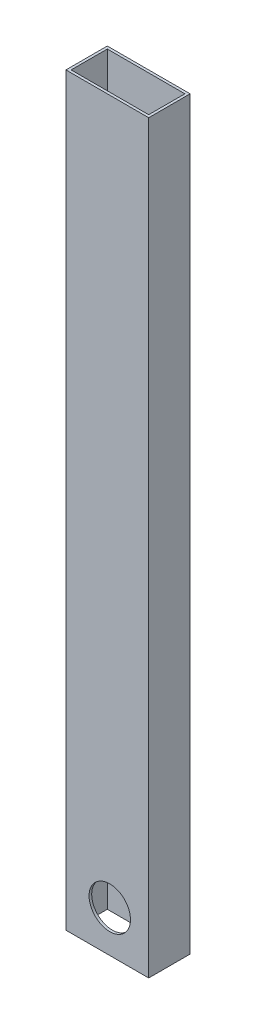
SolidWorks part; units mm, degrees
ref_plane "Front Plane" through (0, 0, 0) normal (0, 0, 1) x (1, 0, 0)
ref_plane "Top Plane" through (0, 0, 0) normal (0, 1, 0) x (1, 0, 0)
ref_plane "Right Plane" through (0, 0, 0) normal (1, 0, 0) x (0, 0, -1)
sketch "Sketch1" plane through (0, 0, 0) normal (0, 1, 0) x (1, 0, 0)
  line L1 (25.4, -12.7) -> (-25.4, -12.7)
  line L2 (25.4, -12.7) -> (25.4, 12.7)
  line L3 (25.4, 12.7) -> (-25.4, 12.7)
  line L4 (-25.4, -12.7) -> (-25.4, 12.7)
  line L5 (25.4, -12.7) -> (-25.4, 12.7) construction
  line L6 (25.4, 12.7) -> (-25.4, -12.7) construction
  line L7 (23.8125, -11.1125) -> (-23.8125, -11.1125)
  line L8 (23.8125, -11.1125) -> (23.8125, 11.1125)
  line L9 (23.8125, 11.1125) -> (-23.8125, 11.1125)
  line L10 (-23.8125, -11.1125) -> (-23.8125, 11.1125)
  line L11 (23.8125, -11.1125) -> (-23.8125, 11.1125) construction
  line L12 (23.8125, 11.1125) -> (-23.8125, -11.1125) construction
  point P0 (0, 0)
  point P6 (0, 0)
  dimension "D1" = 1.5875
  dimension "D2" = 1.5875
  dimension "D3" = 50.8
  dimension "D4" = 25.4
extrude "Boss-Extrude1" add sketch "Sketch1" along normal blind 457.2
sketch "Sketch2" plane through (0, 0, -12.7) normal (0, 0, -1) x (-1, 0, 0)
  line L0 (-1.524, 0) -> (-1.524, 25.4) construction
  line L1 (-25.4, 0) -> (25.4, 0) construction
  line L2 (-25.4, 457.2) -> (-25.4, 0) construction
  circle A1 centre (-1.524, 25.4) radius 12.7
  dimension "D2" = 25.4
  dimension "D3" = 25.4
  dimension "D1" = 23.876
extrude "Cut-Extrude1" cut sketch "Sketch2" against normal blind 457.2
